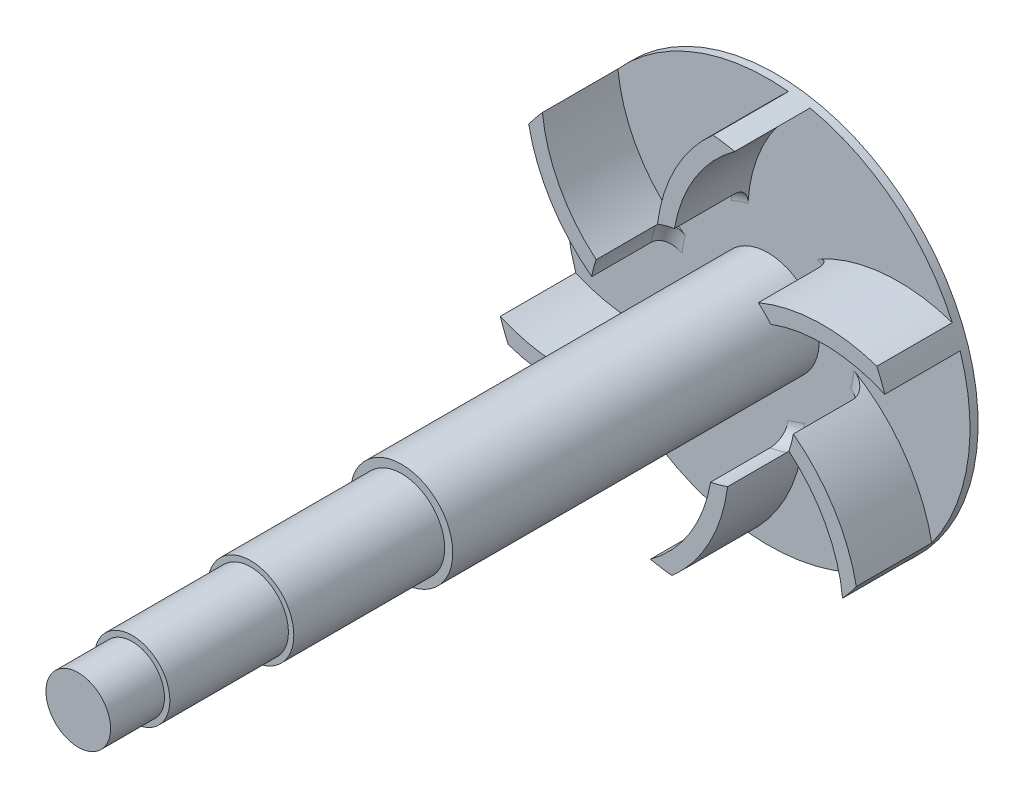
SolidWorks part; units mm, degrees
ref_plane "Front Plane" through (0, 0, 0) normal (0, 0, 1) x (1, 0, 0)
ref_plane "Top Plane" through (0, 0, 0) normal (0, 1, 0) x (1, 0, 0)
ref_plane "Right Plane" through (0, 0, 0) normal (1, 0, 0) x (0, 0, -1)
sketch "Sketch1" plane through (0, 0, 0) normal (0, 0, 1) x (1, 0, 0)
  circle A0 centre (0, 0) radius 9.5
  dimension "D1" = 19
extrude "Boss-Extrude1" add sketch "Sketch1" along normal blind 68
sketch "Sketch2" plane through (0, 0, 68) normal (0, 0, 1) x (1, 0, 0)
  circle A0 centre (0, 0) radius 8
extrude "Boss-Extrude2" add sketch "Sketch2" along normal blind 28
sketch "Sketch3" plane through (0, 0, 96) normal (0, 0, 1) x (1, 0, 0)
  circle A0 centre (0, 0) radius 7
extrude "Boss-Extrude3" add sketch "Sketch3" along normal blind 22
sketch "Sketch4" plane through (0, 0, 118) normal (0, 0, 1) x (1, 0, 0)
  circle A0 centre (0, 0) radius 6
extrude "Boss-Extrude4" add sketch "Sketch4" along normal blind 10
sketch "Sketch5" plane through (0, 0, 0) normal (0, 0, -1) x (-1, 0, 0)
  circle A0 centre (0, 0) radius 37.5
  dimension "D1" = 75
extrude "Boss-Extrude5" add sketch "Sketch5" along normal blind 1.5
sketch "Sketch6" plane through (0, 0, -1.5) normal (0, 0, -1) x (-1, 0, 0)
  circle A0 centre (0, 0) radius 12.5
  circle A1 centre (0, 0) radius 7
extrude "Boss-Extrude6" add sketch "Sketch6" along normal blind 17.5
fillet "Fillet1" radius 6 1 edges at (-12.5, 0, -1.5)
sketch "Sketch8" plane through (0, 0, 0) normal (0, 0, 1) x (1, 0, 0)
  arc A0 (-14.5193, -12.2552) -> (-12.2024, -14.5637) centre (0, 0) ccw
  arc A2 (7.822, 36.6752) -> (-3.3537, 18.7017) centre (24.2487, 14) ccw
  arc A3 (-27.8506, 25.1116) -> (-17.873, 6.4464) centre (0, 28) ccw
  arc A4 (-30.4041, 21.9509) -> (-18.7137, 3.2857) centre (0, 28) ccw
  arc A5 (-27.8506, 25.1116) -> (-30.4041, 21.9509) centre (0, 0) ccw
  arc A6 (3.808, 37.3062) -> (-6.5114, 17.8494) centre (24.2487, 14) ccw
  arc A7 (35.6726, 11.5635) -> (14.5193, 12.2552) centre (24.2487, -14) ccw
  arc A8 (34.2121, 15.3553) -> (12.2024, 14.5637) centre (24.2487, -14) ccw
  arc A9 (27.8506, -25.1116) -> (17.873, -6.4464) centre (0, -28) ccw
  arc A10 (30.4041, -21.9509) -> (18.7137, -3.2857) centre (0, -28) ccw
  arc A11 (-7.822, -36.6752) -> (3.3537, -18.7017) centre (-24.2487, -14) ccw
  arc A12 (-3.808, -37.3062) -> (6.5114, -17.8494) centre (-24.2487, -14) ccw
  arc A13 (-35.6726, -11.5635) -> (-14.5193, -12.2552) centre (-24.2487, 14) ccw
  arc A14 (-34.2121, -15.3553) -> (-12.2024, -14.5637) centre (-24.2487, 14) ccw
  arc A15 (7.822, 36.6752) -> (3.808, 37.3062) centre (0, 0) ccw
  arc A16 (35.6726, 11.5635) -> (34.2121, 15.3553) centre (0, 0) ccw
  arc A17 (27.8506, -25.1116) -> (30.4041, -21.9509) centre (0, 0) ccw
  arc A18 (-7.822, -36.6752) -> (-3.808, -37.3062) centre (0, 0) ccw
  arc A19 (-35.6726, -11.5635) -> (-34.2121, -15.3553) centre (0, 0) ccw
  arc A20 (-17.873, 6.4464) -> (-18.7137, 3.2857) centre (0, 0) ccw
  arc A23 (-3.3537, 18.7017) -> (-6.5114, 17.8494) centre (0, 0) ccw
  arc A24 (14.5193, 12.2552) -> (12.2024, 14.5637) centre (0, 0) ccw
  arc A27 (17.873, -6.4464) -> (18.7137, -3.2857) centre (0, 0) ccw
  arc A28 (3.3537, -18.7017) -> (6.5114, -17.8494) centre (0, 0) ccw
  point P38 (0, 0)
  dimension "D3" = 6
extrude "Boss-Extrude7" add sketch "Sketch8" along normal blind 14
fillet "Fillet2" radius 3 6 edges at (-4.9509, 18.3436, 0) (13.4106, 13.4594, 0) (18.3615, -4.8842, 0) (4.9509, -18.3436, 0) (-18.3615, 4.8842, 0) (-13.4106, -13.4594, 0)
